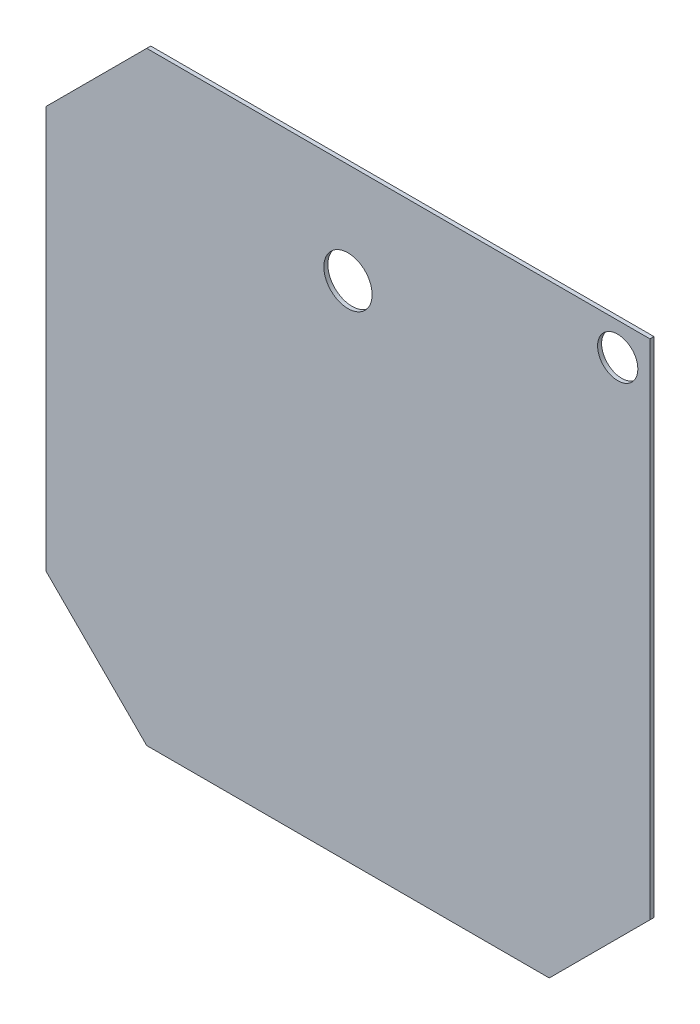
SolidWorks part; units mm, degrees
ref_plane "Front Plane" through (0, 0, 0) normal (0, 0, 1) x (1, 0, 0)
ref_plane "Top Plane" through (0, 0, 0) normal (0, 1, 0) x (1, 0, 0)
ref_plane "Right Plane" through (0, 0, 0) normal (1, 0, 0) x (0, 0, -1)
sketch "Sketch1" plane through (0, 0, 0) normal (0, 0, 1) x (1, 0, 0)
  line L0 (-75, 50) -> (-50, 75)
  line L1 (-50, 75) -> (75, 75)
  line L2 (-75, 50) -> (-75, -50)
  line L3 (-50, -75) -> (50, -75)
  line L4 (75, -50) -> (75, 75)
  line L5 (0, 75) -> (0, -75) construction
  line L6 (-75, 0) -> (75, 0) construction
  line L8 (75, -50) -> (50, -75)
  line L9 (-75, -50) -> (-50, -75)
  circle A0 centre (0, 50) radius 6
  dimension "D1" = 12
  dimension "D3" = 135
extrude "Boss-Extrude1" add sketch "Sketch1" along normal blind 1
sketch "Sketch2" plane through (0, 0, 1) normal (0, 0, 1) x (1, 0, 0)
  line L0 (75, 75) -> (-50, 75) construction
  line L2 (75, -50) -> (75, 75) construction
  circle A0 centre (67, 67) radius 5
  dimension "D1" = 10
  dimension "D2" = 8
  dimension "D3" = 8
extrude "Cut-Extrude1" cut sketch "Sketch2" against normal blind 10
